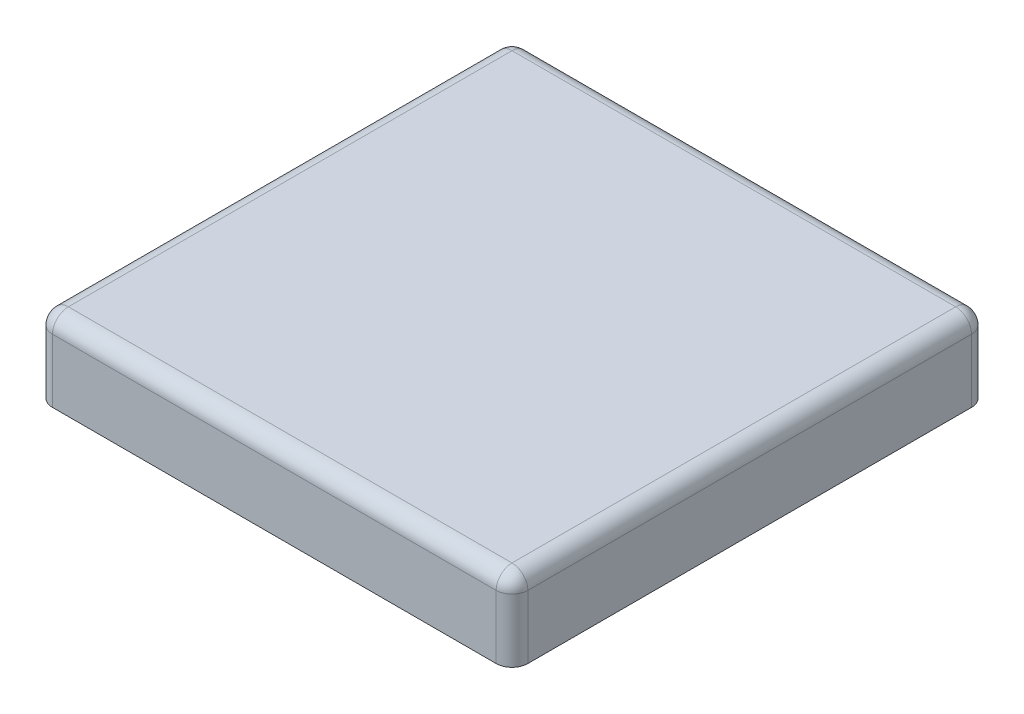
SolidWorks part; units mm, degrees
ref_plane "Front Plane" through (0, 0, 0) normal (0, 0, 1) x (1, 0, 0)
ref_plane "Top Plane" through (0, 0, 0) normal (0, 1, 0) x (1, 0, 0)
ref_plane "Right Plane" through (0, 0, 0) normal (1, 0, 0) x (0, 0, -1)
sketch "Sketch1" plane through (0, 0, 0) normal (0, 1, 0) x (1, 0, 0)
  line L1 (150, -150) -> (-150, -150)
  line L2 (150, -150) -> (150, 150)
  line L3 (150, 150) -> (-150, 150)
  line L4 (-150, -150) -> (-150, 150)
  line L5 (150, -150) -> (-150, 150) construction
  line L6 (150, 150) -> (-150, -150) construction
  point P0 (0, 0)
  dimension "D1" = 300
  dimension "D2" = 300
extrude "Boss-Extrude1" add sketch "Sketch1" along normal blind 50
fillet "Fillet1" radius 10 8 edges at (150, 50, 0) (0, 50, 150) (-150, 50, 0) (0, 50, -150) (-150, 25, -150) (150, 25, -150) (150, 25, 150) (-150, 25, 150)
